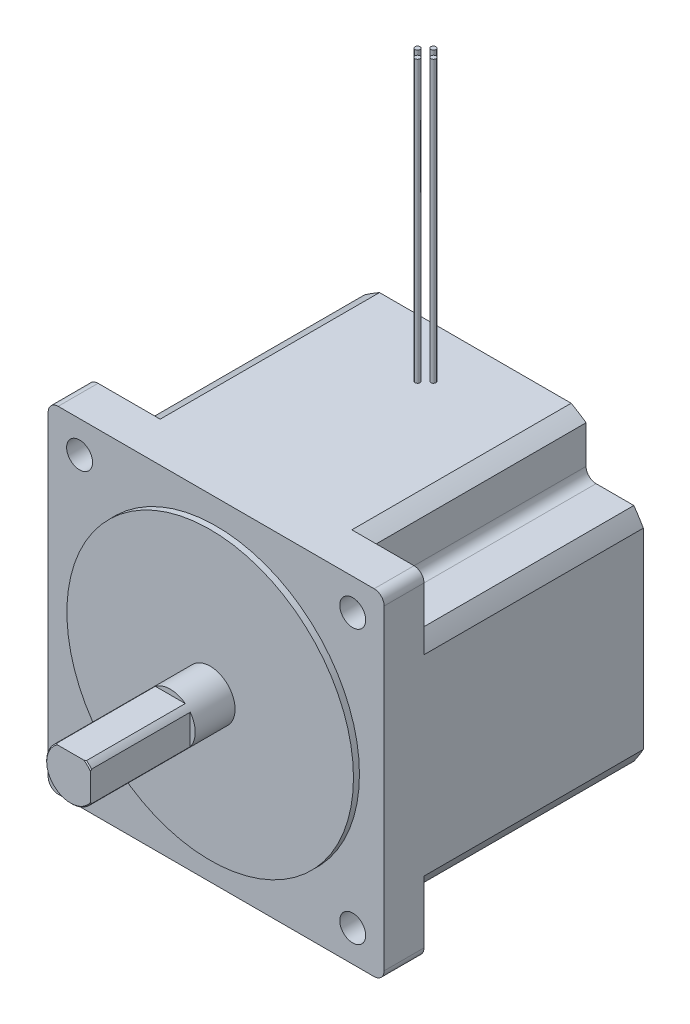
SolidWorks part; units mm, degrees
material "Plain Carbon Steel"
ref_plane "Front Plane" through (0, 0, 0) normal (0, 0, 1) x (1, 0, 0)
ref_plane "Top Plane" through (0, 0, 0) normal (0, 1, 0) x (1, 0, 0)
ref_plane "Right Plane" through (0, 0, 0) normal (1, 0, 0) x (0, 0, -1)
ref_plane "Plane1" through (0, 0, 66.04) normal (0, 0, 1) x (1, 0, 0)
sketch "Sketch1" plane through (0, 0, 66.04) normal (0, 0, 1) x (1, 0, 0)
  line L0 (42.799, -42.799) -> (42.799, 42.799)
  line L1 (42.799, 42.799) -> (-42.799, 42.799)
  line L2 (-42.799, 42.799) -> (-42.799, -42.799)
  line L3 (-42.799, -42.799) -> (42.799, -42.799)
extrude "Boss-Extrude1" add sketch "Sketch1" against normal blind 66.04
sketch "Sketch2" plane through (0, 0, 0) normal (0, 0, -1) x (-1, 0, 0)
  line L0 (-42.799, -42.799) -> (-24.4207, -42.799)
  line L1 (-42.799, -24.4207) -> (-42.799, -42.799)
  arc A0 (-24.4207, -42.799) -> (-42.799, -24.4207) centre (0, 0) cw
extrude "Cut-Extrude1" cut sketch "Sketch2" against normal blind 55.88
sketch "Sketch3" plane through (0, 0, 0) normal (0, 0, -1) x (-1, 0, 0)
  line L0 (-28.2194, -40.3954) -> (-28.2194, -28.2194)
  line L1 (-28.2194, -28.2194) -> (-40.3954, -28.2194)
  arc A0 (-40.3954, -28.2194) -> (-28.2194, -40.3954) centre (0, 0) ccw
extrude "Cut-Extrude2" cut sketch "Sketch3" against normal blind 55.88
sketch "Sketch4" plane through (0, 0, 0) normal (0, 0, -1) x (-1, 0, 0)
  line L0 (-42.799, 42.799) -> (-42.799, 24.4207)
  line L1 (-24.4207, 42.799) -> (-42.799, 42.799)
  arc A0 (-42.799, 24.4207) -> (-24.4207, 42.799) centre (0, 0) cw
extrude "Cut-Extrude3" cut sketch "Sketch4" against normal blind 55.88
sketch "Sketch5" plane through (0, 0, 0) normal (0, 0, -1) x (-1, 0, 0)
  line L0 (-40.3954, 28.2194) -> (-28.2194, 28.2194)
  line L1 (-28.2194, 28.2194) -> (-28.2194, 40.3954)
  arc A0 (-28.2194, 40.3954) -> (-40.3954, 28.2194) centre (0, 0) ccw
extrude "Cut-Extrude4" cut sketch "Sketch5" against normal blind 55.88
sketch "Sketch6" plane through (0, 0, 0) normal (0, 0, -1) x (-1, 0, 0)
  line L0 (42.799, 42.799) -> (24.4207, 42.799)
  line L1 (42.799, 24.4207) -> (42.799, 42.799)
  arc A0 (24.4207, 42.799) -> (42.799, 24.4207) centre (0, 0) cw
extrude "Cut-Extrude5" cut sketch "Sketch6" against normal blind 55.88
sketch "Sketch7" plane through (0, 0, 0) normal (0, 0, -1) x (-1, 0, 0)
  line L0 (28.2194, 40.3954) -> (28.2194, 28.2194)
  line L1 (28.2194, 28.2194) -> (40.3954, 28.2194)
  arc A0 (40.3954, 28.2194) -> (28.2194, 40.3954) centre (0, 0) ccw
extrude "Cut-Extrude6" cut sketch "Sketch7" against normal blind 55.88
sketch "Sketch8" plane through (0, 0, 0) normal (0, 0, -1) x (-1, 0, 0)
  line L0 (42.799, -42.799) -> (42.799, -24.4207)
  line L1 (24.4207, -42.799) -> (42.799, -42.799)
  arc A0 (42.799, -24.4207) -> (24.4207, -42.799) centre (0, 0) cw
extrude "Cut-Extrude7" cut sketch "Sketch8" against normal blind 55.88
sketch "Sketch9" plane through (0, 0, 0) normal (0, 0, -1) x (-1, 0, 0)
  line L0 (40.3954, -28.2194) -> (28.2194, -28.2194)
  line L1 (28.2194, -28.2194) -> (28.2194, -40.3954)
  arc A0 (28.2194, -40.3954) -> (40.3954, -28.2194) centre (0, 0) ccw
extrude "Cut-Extrude8" cut sketch "Sketch9" against normal blind 55.88
sketch "Sketch10" plane through (0, 0, 66.04) normal (0, 0, 1) x (1, 0, 0)
  circle A0 centre (0, 0) radius 36.5125
extrude "Boss-Extrude2" add sketch "Sketch10" along normal blind 1.524
sketch "Sketch11" plane through (0, 0, 67.564) normal (0, 0, 1) x (1, 0, 0)
  circle A0 centre (0, 0) radius 6.35
extrude "Boss-Extrude3" add sketch "Sketch11" along normal blind 35.56
sketch "Sketch12" plane through (0, 0, 103.124) normal (0, 0, 1) x (1, 0, 0)
  line L0 (-3.81, 5.08) -> (3.81, 5.08)
  arc A0 (3.81, 5.08) -> (-3.81, 5.08) centre (0, 0) ccw
extrude "Cut-Extrude9" cut sketch "Sketch12" against normal blind 25.4
sketch "Sketch13" plane through (0, 0, 103.124) normal (0, 0, 1) x (1, 0, 0)
  line L0 (5.08, 3.81) -> (5.08, -3.81)
  arc A0 (5.08, -3.81) -> (5.08, 3.81) centre (0, 0) ccw
extrude "Cut-Extrude10" cut sketch "Sketch13" against normal blind 25.4
ref_plane "Plane2" through (0, 0, 12.7) normal (0, 0, -1) x (-1, 0, 0)
sketch "Sketch14" plane through (0, 0, 12.7) normal (0, 0, -1) x (-1, 0, 0)
  line L0 (1.397, 42.799) -> (2.032, 42.799)
  line L1 (2.032, 42.799) -> (2.032, 114.3)
  line L2 (2.032, 114.3) -> (1.397, 114.3)
  line L3 (1.397, 114.3) -> (1.397, 42.799)
  line L4 (2.032, 42.799) -> (2.032, 114.3) construction
revolve "Revolve1" add sketch "Sketch14" angle 360 about L4
sketch "Sketch15" plane through (0, 0, 12.7) normal (0, 0, -1) x (-1, 0, 0)
  line L0 (-2.667, 42.799) -> (-2.032, 42.799)
  line L1 (-2.032, 42.799) -> (-2.032, 114.3)
  line L2 (-2.032, 114.3) -> (-2.667, 114.3)
  line L3 (-2.667, 114.3) -> (-2.667, 42.799)
  line L4 (-2.032, 42.799) -> (-2.032, 114.3) construction
revolve "Revolve2" add sketch "Sketch15" angle 360 about L4
ref_plane "Plane3" through (0, 0, 14.732) normal (0, 0, -1) x (-1, 0, 0)
sketch "Sketch16" plane through (0, 0, 14.732) normal (0, 0, -1) x (-1, 0, 0)
  line L0 (-0.635, 42.799) -> (0, 42.799)
  line L1 (0, 42.799) -> (0, 114.3)
  line L2 (0, 114.3) -> (-0.635, 114.3)
  line L3 (-0.635, 114.3) -> (-0.635, 42.799)
  line L4 (0, 42.799) -> (0, 114.3) construction
revolve "Revolve3" add sketch "Sketch16" angle 360 about L4
ref_plane "Plane4" through (0, 0, 10.668) normal (0, 0, -1) x (-1, 0, 0)
sketch "Sketch17" plane through (0, 0, 10.668) normal (0, 0, -1) x (-1, 0, 0)
  line L0 (-0.635, 42.799) -> (0, 42.799)
  line L1 (0, 42.799) -> (0, 114.3)
  line L2 (0, 114.3) -> (-0.635, 114.3)
  line L3 (-0.635, 114.3) -> (-0.635, 42.799)
  line L4 (0, 42.799) -> (0, 114.3) construction
revolve "Revolve4" add sketch "Sketch17" angle 360 about L4
hole_wizard "Hole1" positions "Sketch19" profile "Sketch18" legacy
sketch "Sketch19" plane through (0, 0, 55.88) normal (0, 0, -1) x (-1, 0, 0)
  point P0 (34.798, -34.798)
sketch "Sketch18" plane through (-34.798, -34.798, 55.88) normal (1, 0, 0) x (0, 1, 0)
  line L0 (0, 0) -> (0, 47.244)
  line L1 (0, 47.244) -> (3.302, 47.244)
  line L2 (3.302, 47.244) -> (3.302, 0)
  line L3 (3.302, 0) -> (0, 0)
  line L4 (0, 110) -> (0, -10) construction
  dimension "Diameter" = 6.604
  dimension "Depth" = 47.244
hole_wizard "Hole2" positions "Sketch21" profile "Sketch20" legacy
sketch "Sketch21" plane through (0, 0, 55.88) normal (0, 0, -1) x (-1, 0, 0)
  point P0 (34.798, 34.798)
sketch "Sketch20" plane through (-34.798, 34.798, 55.88) normal (1, 0, 0) x (0, 1, 0)
  line L0 (0, 0) -> (0, 47.244)
  line L1 (0, 47.244) -> (3.302, 47.244)
  line L2 (3.302, 47.244) -> (3.302, 0)
  line L3 (3.302, 0) -> (0, 0)
  line L4 (0, 110) -> (0, -10) construction
  dimension "Diameter" = 6.604
  dimension "Depth" = 47.244
hole_wizard "Hole3" positions "Sketch23" profile "Sketch22" legacy
sketch "Sketch23" plane through (0, 0, 55.88) normal (0, 0, -1) x (-1, 0, 0)
  point P0 (-34.798, 34.798)
sketch "Sketch22" plane through (34.798, 34.798, 55.88) normal (1, 0, 0) x (0, 1, 0)
  line L0 (0, 0) -> (0, 47.244)
  line L1 (0, 47.244) -> (3.302, 47.244)
  line L2 (3.302, 47.244) -> (3.302, 0)
  line L3 (3.302, 0) -> (0, 0)
  line L4 (0, 110) -> (0, -10) construction
  dimension "Diameter" = 6.604
  dimension "Depth" = 47.244
hole_wizard "Hole4" positions "Sketch25" profile "Sketch24" legacy
sketch "Sketch25" plane through (0, 0, 55.88) normal (0, 0, -1) x (-1, 0, 0)
  point P0 (-34.798, -34.798)
sketch "Sketch24" plane through (34.798, -34.798, 55.88) normal (1, 0, 0) x (0, 1, 0)
  line L0 (0, 0) -> (0, 47.244)
  line L1 (0, 47.244) -> (3.302, 47.244)
  line L2 (3.302, 47.244) -> (3.302, 0)
  line L3 (3.302, 0) -> (0, 0)
  line L4 (0, 110) -> (0, -10) construction
  dimension "Diameter" = 6.604
  dimension "Depth" = 47.244
chamfer "Chamfer1" distance 0.254 angle 45 1 edges at (-4.4901, -4.4901, 103.124)
chamfer "Chamfer2" distance 0.254 angle 45 1 edges at (4.4901, 4.4901, 103.124)
fillet "Fillet1" radius 2.54 1 edges at (-42.799, -42.799, 60.96)
fillet "Fillet2" radius 2.54 1 edges at (-42.799, 42.799, 60.96)
fillet "Fillet3" radius 2.54 1 edges at (42.799, 42.799, 60.96)
fillet "Fillet4" radius 2.54 1 edges at (-28.2194, 28.2194, 27.94)
fillet "Fillet5" radius 2.54 1 edges at (42.799, -42.799, 60.96)
fillet "Fillet6" radius 2.54 1 edges at (28.2194, -28.2194, 27.94)
fillet "Fillet7" radius 2.54 1 edges at (28.2194, 28.2194, 27.94)
fillet "Fillet8" radius 2.54 1 edges at (-28.2194, -28.2194, 27.94)
